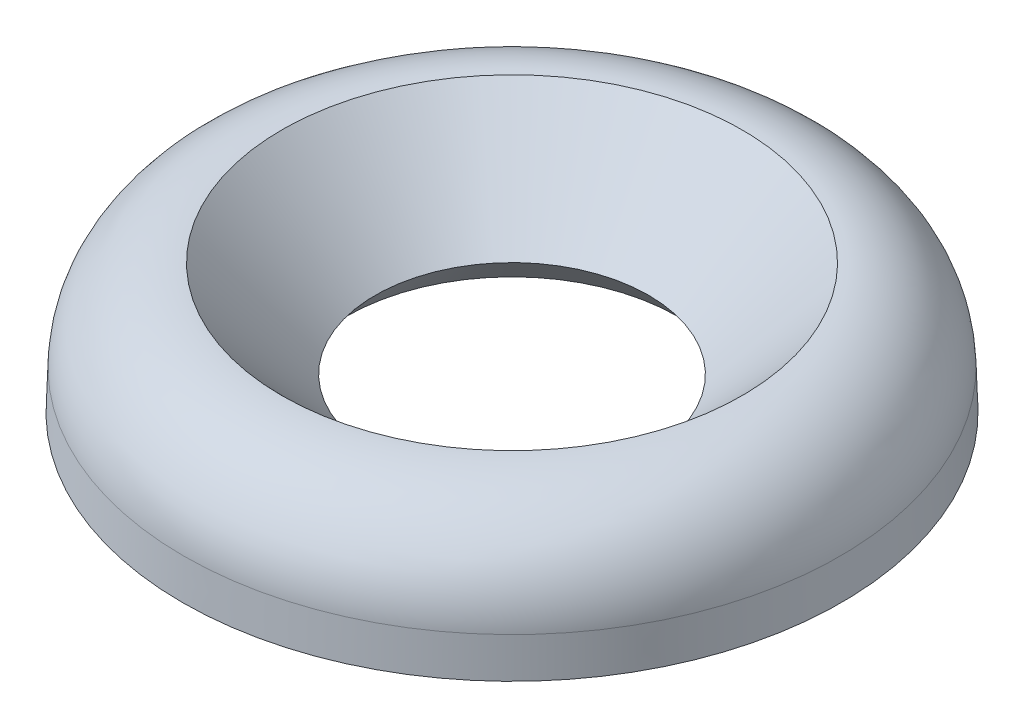
SolidWorks part; units mm, degrees
ref_plane "Front Plane" through (0, 0, 0) normal (0, 0, 1) x (1, 0, 0)
ref_plane "Top Plane" through (0, 0, 0) normal (0, 1, 0) x (1, 0, 0)
ref_plane "Right Plane" through (0, 0, 0) normal (1, 0, 0) x (0, 0, -1)
sketch "Sketch2" plane through (0, 0, 0) normal (0, 0, 1) x (1, 0, 0)
  line L0 (-8.871, 4.9911) -> (-5.2705, 1.27)
  line L1 (-12.7, 0) -> (-12.6468, 1.5231)
  line L2 (-12.7, 0) -> (-6.3924, 0)
  line L3 (-6.3924, 0) -> (-5.2705, 1.27)
  line L4 (0, 9.1852) -> (0, -5.5527) construction
  arc A0 (-12.6468, 1.5231) -> (-8.871, 4.9911) centre (-9.0509, 1.3975) cw
  dimension "D1" = 12.7
  dimension "D2" = 8.871
  dimension "D3" = 4.9911
  dimension "D4" = 5.2705
  dimension "D5" = 1.27
  dimension "D6" = 1.524
  dimension "D7" = 88
revolve "Revolve1" add sketch "Sketch2" angle 360 about L4
